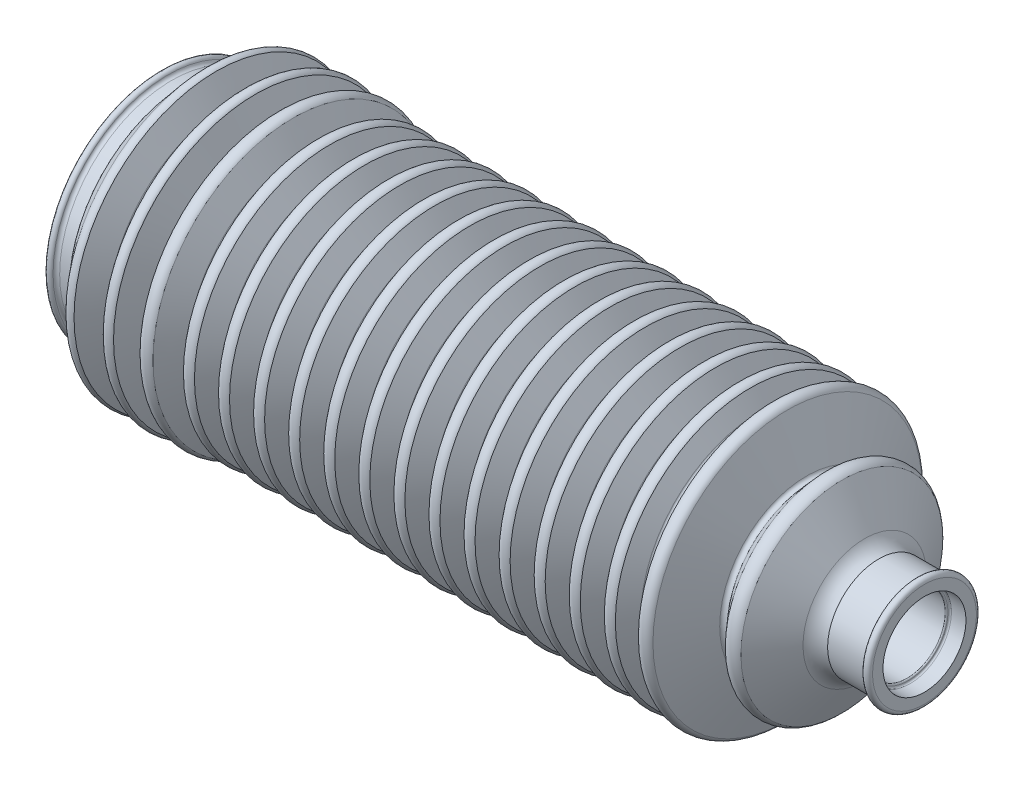
SolidWorks part; units mm, degrees
material "HYPALON"
ref_plane "Front Plane" through (0, 0, 0) normal (0, 0, 1) x (1, 0, 0)
ref_plane "Top Plane" through (0, 0, 0) normal (0, 1, 0) x (1, 0, 0)
ref_plane "Right Plane" through (0, 0, 0) normal (1, 0, 0) x (0, 0, -1)
sketch "Sketch1" plane through (0, 0, 0) normal (0, 0, 1) x (1, 0, 0)
  line L0 (0, 29.3759) -> (0, 0) construction
  line L1 (3.2214, 33.8788) -> (7.0702, 33.8788)
  line L2 (209.8069, 11.5) -> (225.25, 11.5)
  line L3 (226.1148, 12.5257) -> (230.5117, 12.5257)
  line L4 (230.5117, 15.6781) -> (230.5117, 12.5257)
  line L5 (227.9064, 15.4083) -> (216.6704, 15.4083)
  line L6 (8.7209, 28.5431) -> (0.9958, 28.5431)
  line L7 (0, 34.21) -> (0, 29.3759)
  line L8 (0, 0) -> (226.9169, 0) construction
  line L9 (43.9932, 32.2805) -> (177.5477, 32.2805) construction
  line L10 (50.8885, 40.8383) -> (54.0155, 35.4192)
  line L11 (55.0622, 35.3422) -> (57.894, 40.508)
  line L12 (61.4807, 40.8383) -> (64.6077, 35.4192)
  line L13 (49.9549, 38.4963) -> (52.6485, 33.1303)
  line L14 (56.4737, 33.2334) -> (59.2464, 38.439)
  line L15 (65.6544, 35.3422) -> (68.4862, 40.508)
  line L16 (60.5471, 38.4963) -> (63.2407, 33.1303)
  line L17 (67.0659, 33.2334) -> (69.8386, 38.439)
  line L18 (72.0729, 40.8383) -> (75.1999, 35.4192)
  line L19 (76.2466, 35.3422) -> (79.0784, 40.508)
  line L20 (71.1393, 38.4963) -> (73.8329, 33.1303)
  line L21 (77.6581, 33.2334) -> (80.4308, 38.439)
  line L22 (82.6651, 40.8383) -> (85.7921, 35.4192)
  line L23 (86.8388, 35.3422) -> (89.6706, 40.508)
  line L24 (81.7315, 38.4963) -> (84.4251, 33.1303)
  line L25 (88.2503, 33.2334) -> (91.023, 38.439)
  line L26 (93.2573, 40.8383) -> (96.3843, 35.4192)
  line L27 (97.431, 35.3422) -> (100.2628, 40.508)
  line L28 (92.3237, 38.4963) -> (95.0173, 33.1303)
  line L29 (98.8425, 33.2334) -> (101.6152, 38.439)
  line L30 (103.8496, 40.8383) -> (106.9765, 35.4192)
  line L31 (108.0232, 35.3422) -> (110.855, 40.508)
  line L32 (102.9159, 38.4963) -> (105.6095, 33.1303)
  line L33 (109.4347, 33.2334) -> (112.2074, 38.439)
  line L34 (114.4418, 40.8383) -> (117.5687, 35.4192)
  line L35 (118.6154, 35.3422) -> (121.4472, 40.508)
  line L36 (113.5081, 38.4963) -> (116.2017, 33.1303)
  line L37 (120.0269, 33.2334) -> (122.7996, 38.439)
  line L38 (125.034, 40.8383) -> (128.1609, 35.4192)
  line L39 (129.2076, 35.3422) -> (132.0394, 40.508)
  line L40 (124.1003, 38.4963) -> (126.7939, 33.1303)
  line L41 (130.6191, 33.2334) -> (133.3918, 38.439)
  line L42 (135.6262, 40.8383) -> (138.7531, 35.4192)
  line L43 (7.9107, 35.547) -> (14.1282, 42.9017)
  line L44 (16.6539, 42.9654) -> (20.3122, 36.1831)
  line L45 (22.0723, 36.1241) -> (25.3354, 42.794)
  line L46 (28.4396, 42.8256) -> (31.4672, 35.6905)
  line L47 (32.7295, 35.559) -> (36.0239, 42.4024)
  line L48 (39.8236, 42.302) -> (43.4232, 35.4192)
  line L49 (44.47, 35.3422) -> (47.3018, 40.508)
  line L50 (139.7998, 35.3422) -> (142.6316, 40.508)
  line L51 (9.8304, 31.5125) -> (14.5204, 40.5007)
  line L52 (15.4802, 40.5139) -> (19.6793, 33.0571)
  line L53 (23.5336, 34.0488) -> (26.1168, 40.4451)
  line L54 (27.327, 40.4688) -> (30.3546, 33.2677)
  line L55 (34.3262, 33.358) -> (37.441, 40.2821)
  line L56 (38.5615, 40.1566) -> (42.0563, 33.1303)
  line L57 (45.8815, 33.2334) -> (48.6542, 38.439)
  line L58 (134.6925, 38.4963) -> (137.3861, 33.1303)
  line L59 (177.995, 40.8383) -> (180.7247, 35.9215)
  line L60 (182.1651, 35.8258) -> (185.2683, 41.1544)
  line L61 (189.1472, 40.6282) -> (194.9101, 26.2392)
  line L62 (196.937, 26.0482) -> (201.2606, 30.8976)
  line L63 (205.5712, 30.4841) -> (212.4546, 18.6294)
  line L64 (141.2113, 33.2334) -> (143.984, 38.439)
  line L65 (227.9064, 15.4083) -> (228.4405, 16.5186)
  line L66 (146.2184, 40.8383) -> (149.3453, 35.4192)
  line L67 (177.0613, 38.4963) -> (179.4609, 33.3099)
  line L68 (183.9638, 33.6822) -> (186.1691, 38.0745)
  line L69 (187.386, 38.0617) -> (193.7953, 23.4227)
  line L70 (198.9738, 23.7215) -> (202.0974, 28.0842)
  line L71 (203.9001, 27.657) -> (208.9343, 14.6581)
  line L72 (150.392, 35.3422) -> (153.2238, 40.508)
  line L73 (145.2847, 38.4963) -> (147.9783, 33.1303)
  line L74 (49.1752, 41.5525) -> (135.6485, 41.5525) construction
  line L75 (151.8035, 33.2334) -> (154.5762, 38.439)
  line L76 (156.8106, 40.8383) -> (159.9375, 35.4192)
  line L77 (160.9842, 35.3422) -> (163.816, 40.508)
  line L78 (155.8769, 38.4963) -> (158.5705, 33.1303)
  line L79 (162.3957, 33.2334) -> (165.1684, 38.439)
  line L80 (167.4028, 40.8383) -> (170.5297, 35.4192)
  line L81 (171.5764, 35.3422) -> (174.4082, 40.508)
  line L82 (166.4691, 38.4963) -> (169.1627, 33.1303)
  line L83 (172.9879, 33.2334) -> (175.7606, 38.439)
  arc A0 (2.0329, 34.6839) -> (3.2214, 33.8788) centre (3.0922, 34.9678) ccw
  arc A1 (55.0622, 35.3422) -> (54.0155, 35.4192) centre (54.5566, 35.6228) cw
  arc A2 (57.894, 40.508) -> (61.4807, 40.8383) centre (59.8174, 39.2605) cw
  arc A3 (56.4737, 33.2334) -> (52.6485, 33.1303) centre (54.5186, 34.7603) cw
  arc A4 (59.2464, 38.439) -> (60.5471, 38.4963) centre (59.9086, 38.1975) cw
  arc A5 (65.6544, 35.3422) -> (64.6077, 35.4192) centre (65.1488, 35.6228) cw
  arc A6 (68.4862, 40.508) -> (72.0729, 40.8383) centre (70.4096, 39.2605) cw
  arc A7 (67.0659, 33.2334) -> (63.2407, 33.1303) centre (65.1108, 34.7603) cw
  arc A8 (69.8386, 38.439) -> (71.1393, 38.4963) centre (70.5008, 38.1975) cw
  arc A9 (76.2466, 35.3422) -> (75.1999, 35.4192) centre (75.741, 35.6228) cw
  arc A10 (79.0784, 40.508) -> (82.6651, 40.8383) centre (81.0018, 39.2605) cw
  arc A11 (77.6581, 33.2334) -> (73.8329, 33.1303) centre (75.703, 34.7603) cw
  arc A12 (80.4308, 38.439) -> (81.7315, 38.4963) centre (81.093, 38.1975) cw
  arc A13 (86.8388, 35.3422) -> (85.7921, 35.4192) centre (86.3332, 35.6228) cw
  arc A14 (89.6706, 40.508) -> (93.2573, 40.8383) centre (91.594, 39.2605) cw
  arc A15 (88.2503, 33.2334) -> (84.4251, 33.1303) centre (86.2952, 34.7603) cw
  arc A16 (91.023, 38.439) -> (92.3237, 38.4963) centre (91.6853, 38.1975) cw
  arc A17 (97.431, 35.3422) -> (96.3843, 35.4192) centre (96.9254, 35.6228) cw
  arc A18 (100.2628, 40.508) -> (103.8496, 40.8383) centre (102.1862, 39.2605) cw
  arc A19 (98.8425, 33.2334) -> (95.0173, 33.1303) centre (96.8874, 34.7603) cw
  arc A20 (101.6152, 38.439) -> (102.9159, 38.4963) centre (102.2775, 38.1975) cw
  arc A21 (108.0232, 35.3422) -> (106.9765, 35.4192) centre (107.5176, 35.6228) cw
  arc A22 (110.855, 40.508) -> (114.4418, 40.8383) centre (112.7784, 39.2605) cw
  arc A23 (109.4347, 33.2334) -> (105.6095, 33.1303) centre (107.4796, 34.7603) cw
  arc A24 (112.2074, 38.439) -> (113.5081, 38.4963) centre (112.8697, 38.1975) cw
  arc A25 (118.6154, 35.3422) -> (117.5687, 35.4192) centre (118.1099, 35.6228) cw
  arc A26 (121.4472, 40.508) -> (125.034, 40.8383) centre (123.3706, 39.2605) cw
  arc A27 (120.0269, 33.2334) -> (116.2017, 33.1303) centre (118.0718, 34.7603) cw
  arc A28 (122.7996, 38.439) -> (124.1003, 38.4963) centre (123.4619, 38.1975) cw
  arc A29 (129.2076, 35.3422) -> (128.1609, 35.4192) centre (128.7021, 35.6228) cw
  arc A30 (132.0394, 40.508) -> (135.6262, 40.8383) centre (133.9628, 39.2605) cw
  arc A31 (130.6191, 33.2334) -> (126.7939, 33.1303) centre (128.664, 34.7603) cw
  arc A32 (133.3918, 38.439) -> (134.6925, 38.4963) centre (134.0541, 38.1975) cw
  arc A33 (139.7998, 35.3422) -> (138.7531, 35.4192) centre (139.2943, 35.6228) cw
  arc A34 (142.6316, 40.508) -> (146.2184, 40.8383) centre (144.555, 39.2605) cw
  arc A35 (141.2113, 33.2334) -> (137.3861, 33.1303) centre (139.2562, 34.7603) cw
  arc A36 (143.984, 38.439) -> (145.2847, 38.4963) centre (144.6463, 38.1975) cw
  arc A37 (150.392, 35.3422) -> (149.3453, 35.4192) centre (149.8865, 35.6228) cw
  arc A38 (153.2238, 40.508) -> (156.8106, 40.8383) centre (155.1472, 39.2605) cw
  arc A39 (151.8035, 33.2334) -> (147.9783, 33.1303) centre (149.8484, 34.7603) cw
  arc A40 (154.5762, 38.439) -> (155.8769, 38.4963) centre (155.2385, 38.1975) cw
  arc A41 (0.9958, 28.5431) -> (0, 29.3759) centre (0.9402, 29.4883) cw
  arc A42 (9.4439, 30.1434) -> (8.7209, 28.5431) centre (8.2394, 29.7241) cw
  arc A43 (9.4439, 30.1434) -> (9.8304, 31.5125) centre (11.8364, 30.207) cw
  arc A44 (0, 34.21) -> (2.0329, 34.6839) centre (1.042, 34.3375) cw
  arc A45 (7.5149, 34.7283) -> (7.0702, 33.8788) centre (6.5537, 34.6903) cw
  arc A46 (7.5149, 34.7283) -> (7.9107, 35.547) centre (8.4589, 34.777) cw
  arc A47 (14.1282, 42.9017) -> (16.6539, 42.9654) centre (15.4244, 41.6093) cw
  arc A48 (22.0723, 36.1241) -> (20.3122, 36.1831) centre (21.2029, 36.4713) cw
  arc A49 (25.3354, 42.794) -> (28.4396, 42.8256) centre (26.8989, 41.6862) cw
  arc A50 (32.7295, 35.559) -> (31.4672, 35.6905) centre (32.1124, 35.7599) cw
  arc A51 (36.0239, 42.4024) -> (39.8236, 42.302) centre (37.8805, 40.7174) cw
  arc A52 (44.47, 35.3422) -> (43.4232, 35.4192) centre (43.9644, 35.6228) cw
  arc A53 (47.3018, 40.508) -> (50.8885, 40.8383) centre (49.2252, 39.2605) cw
  arc A54 (14.5204, 40.5007) -> (15.4802, 40.5139) centre (15.0028, 40.3283) cw
  arc A55 (23.5336, 34.0488) -> (19.6793, 33.0571) centre (21.3287, 34.6326) cw
  arc A56 (26.1168, 40.4451) -> (27.327, 40.4688) centre (26.7269, 40.2051) cw
  arc A57 (34.3262, 33.358) -> (30.3546, 33.2677) centre (32.3125, 34.5384) cw
  arc A58 (37.441, 40.2821) -> (38.5615, 40.1566) centre (37.9809, 40.0368) cw
  arc A59 (45.8815, 33.2334) -> (42.0563, 33.1303) centre (43.9264, 34.7603) cw
  arc A60 (48.6542, 38.439) -> (49.9549, 38.4963) centre (49.3164, 38.1975) cw
  arc A61 (182.1651, 35.8258) -> (180.7247, 35.9215) centre (181.4597, 36.0972) cw
  arc A62 (185.2683, 41.1544) -> (189.1472, 40.6282) centre (187.0165, 39.4813) cw
  arc A63 (196.937, 26.0482) -> (194.9101, 26.2392) centre (195.9672, 26.6075) cw
  arc A64 (201.2606, 30.8976) -> (205.5712, 30.4841) centre (203.1894, 28.3301) cw
  arc A65 (216.6704, 15.4083) -> (212.4546, 18.6294) centre (218.4137, 22.0593) cw
  arc A66 (228.4405, 16.5186) -> (230.5117, 15.6781) centre (229.3153, 15.7023) cw
  arc A67 (183.9638, 33.6822) -> (179.4609, 33.3099) centre (181.5902, 34.9733) cw
  arc A68 (186.1691, 38.0745) -> (187.386, 38.0617) centre (186.7753, 37.8557) cw
  arc A69 (198.9738, 23.7215) -> (193.7953, 23.4227) centre (196.2605, 25.7221) cw
  arc A70 (202.0974, 28.0842) -> (203.9001, 27.657) centre (202.8785, 27.3632) cw
  arc A71 (208.9343, 14.6581) -> (208.9052, 13.101) centre (207.6724, 13.9029) cw
  arc A72 (209.8069, 11.5) -> (208.9052, 13.101) centre (209.9501, 12.6351) cw
  arc A73 (225.6121, 11.9844) -> (225.25, 11.5) centre (225.1741, 11.9343) cw
  arc A74 (225.6121, 11.9844) -> (226.1148, 12.5257) centre (226.1246, 12.0126) cw
  circle A75 centre (3.2214, 34.5384) radius 0.6596 construction
  arc A76 (160.9842, 35.3422) -> (159.9375, 35.4192) centre (160.4787, 35.6228) cw
  arc A77 (163.816, 40.508) -> (167.4028, 40.8383) centre (165.7394, 39.2605) cw
  arc A78 (162.3957, 33.2334) -> (158.5705, 33.1303) centre (160.4406, 34.7603) cw
  arc A79 (165.1684, 38.439) -> (166.4691, 38.4963) centre (165.8307, 38.1975) cw
  arc A80 (171.5764, 35.3422) -> (170.5297, 35.4192) centre (171.0709, 35.6228) cw
  arc A81 (174.4082, 40.508) -> (177.995, 40.8383) centre (176.3316, 39.2605) cw
  arc A82 (172.9879, 33.2334) -> (169.1627, 33.1303) centre (171.0328, 34.7603) cw
  arc A83 (175.7606, 38.439) -> (177.0613, 38.4963) centre (176.4229, 38.1975) cw
revolve "Revolve1" add sketch "Sketch1" angle 360 about L8
